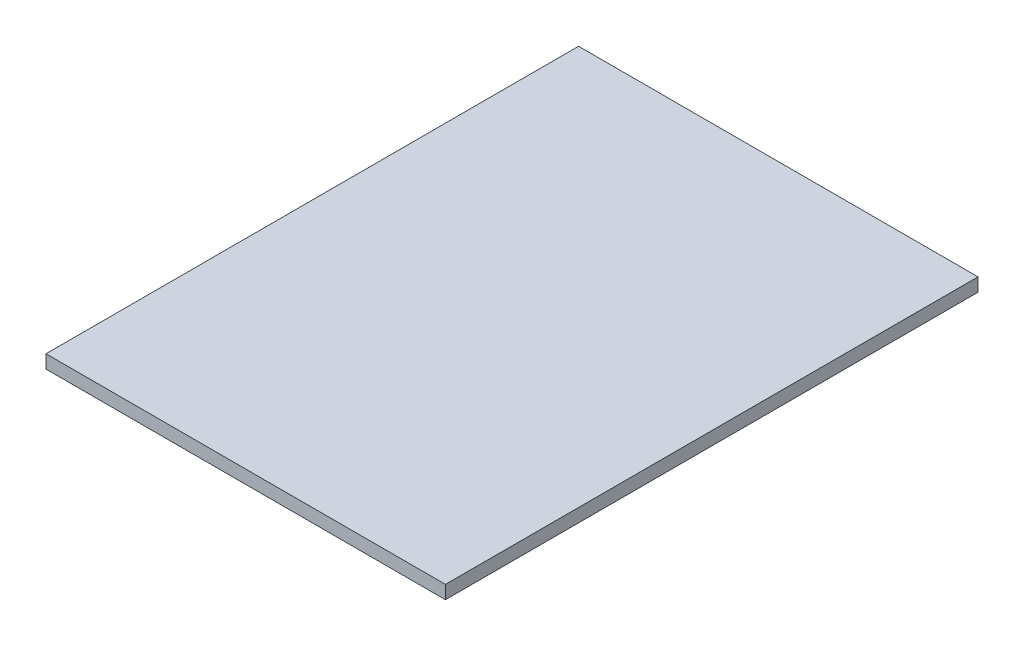
SolidWorks part; units mm, degrees
ref_plane "Plan de face" through (0, 0, 0) normal (0, 0, 1) x (1, 0, 0)
ref_plane "Plan de dessus" through (0, 0, 0) normal (0, 1, 0) x (1, 0, 0)
ref_plane "Plan de droite" through (0, 0, 0) normal (1, 0, 0) x (0, 0, -1)
sketch "Esquisse1" plane through (0, 0, 0) normal (0, 1, 0) x (1, 0, 0)
  line L1 (0, 0) -> (300, 0)
  line L2 (0, 0) -> (0, 400)
  line L3 (0, 400) -> (300, 400)
  line L4 (300, 0) -> (300, 400)
  dimension "D1" = 400
  dimension "D2" = 300
extrude "Extrusion1" add sketch "Esquisse1" along normal blind 10
